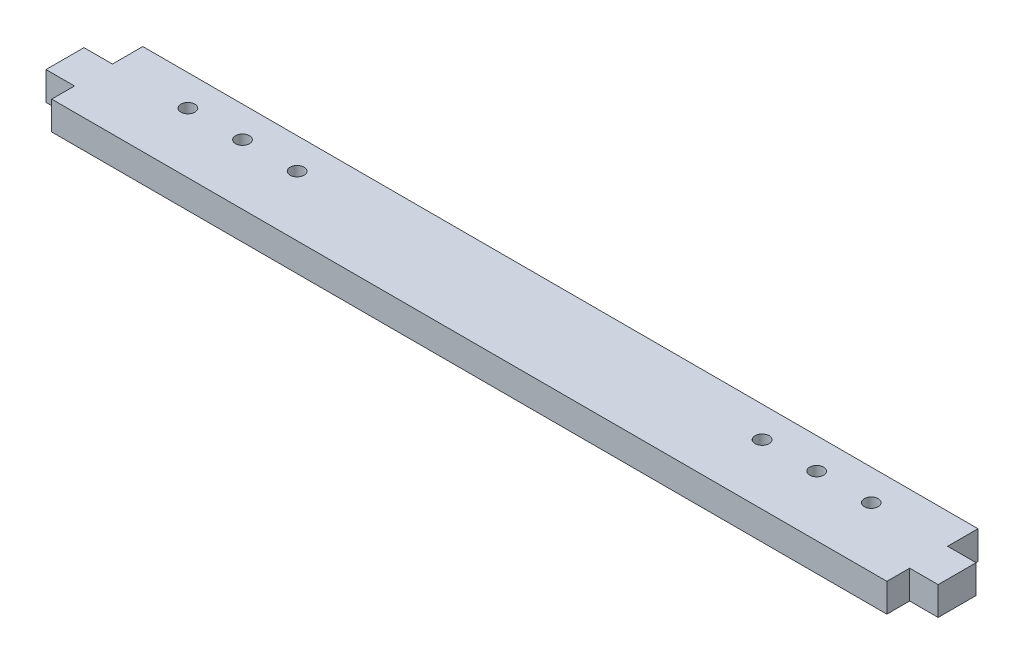
SolidWorks part; units mm, degrees
ref_plane "Front Plane" through (0, 0, 0) normal (0, 0, 1) x (1, 0, 0)
ref_plane "Top Plane" through (0, 0, 0) normal (0, 1, 0) x (1, 0, 0)
ref_plane "Right Plane" through (0, 0, 0) normal (1, 0, 0) x (0, 0, -1)
sketch "Sketch1" plane through (0, 0, 0) normal (0, 1, 0) x (1, 0, 0)
  line L1 (139.7, -15.24) -> (-139.7, -15.24)
  line L2 (139.7, -15.24) -> (139.7, 15.24)
  line L3 (139.7, 15.24) -> (-139.7, 15.24)
  line L4 (-139.7, -15.24) -> (-139.7, 15.24)
  line L5 (139.7, -15.24) -> (-139.7, 15.24) construction
  line L6 (139.7, 15.24) -> (-139.7, -15.24) construction
  point P0 (0, 0)
  dimension "D1" = 279.4
  dimension "D2" = 30.48
extrude "Boss-Extrude1" add sketch "Sketch1" along normal blind 9.525
sketch "Sketch2" plane through (139.7, 0, 0) normal (1, 0, 0) x (0, 0, -1)
  line L0 (-15.24, 0) -> (15.24, 0) construction
  line L1 (-7.62, 0) -> (5.08, 0)
  line L2 (-7.62, 0) -> (-7.62, 9.525)
  line L3 (-7.62, 9.525) -> (5.08, 9.525)
  line L4 (5.08, 0) -> (5.08, 9.525)
  line L5 (-15.24, 9.525) -> (15.24, 9.525) construction
  line L7 (15.24, 9.525) -> (15.24, 0) construction
  dimension "D1" = 12.7
  dimension "D2" = 10.16
extrude "Boss-Extrude2" add sketch "Sketch2" along normal blind 9.525
mirror "Mirror1" about plane through (0, 0, 0) normal (1, 0, 0) of "Boss-Extrude2"
sketch "Sketch3" plane through (0, 0, 0) normal (0, -1, 0) x (1, 0, 0)
  line L0 (139.7, -5.08) -> (139.7, -15.24) construction
  line L1 (139.7, -15.24) -> (-139.7, -15.24) construction
  line L2 (114.3, -15.24) -> (77.7748, -15.24) construction
  line L3 (114.3, -15.24) -> (114.3, -4.9276) construction
  line L4 (114.3, -4.9276) -> (77.7748, -4.9276) construction
  line L5 (77.7748, -15.24) -> (77.7748, -4.9276) construction
  line L6 (114.3, -15.24) -> (77.7748, -4.9276) construction
  line L7 (114.3, -4.9276) -> (77.7748, -15.24) construction
  circle A0 centre (114.3, -4.9276) radius 2.3368
  circle A1 centre (77.7748, -4.9276) radius 2.3368
  circle A2 centre (96.0374, -4.9276) radius 2.3368
  point P6 (96.0374, -10.0838)
  dimension "D4" = 4.6736
  dimension "D5" = 4.6736
  dimension "D6" = 4.6736
  dimension "D1" = 36.5252
  dimension "D2" = 10.3124
  dimension "D3" = 25.4
extrude "Cut-Extrude1" cut sketch "Sketch3" against normal through all
mirror "Mirror2" about plane through (0, 0, 0) normal (1, 0, 0) of "Cut-Extrude1"
